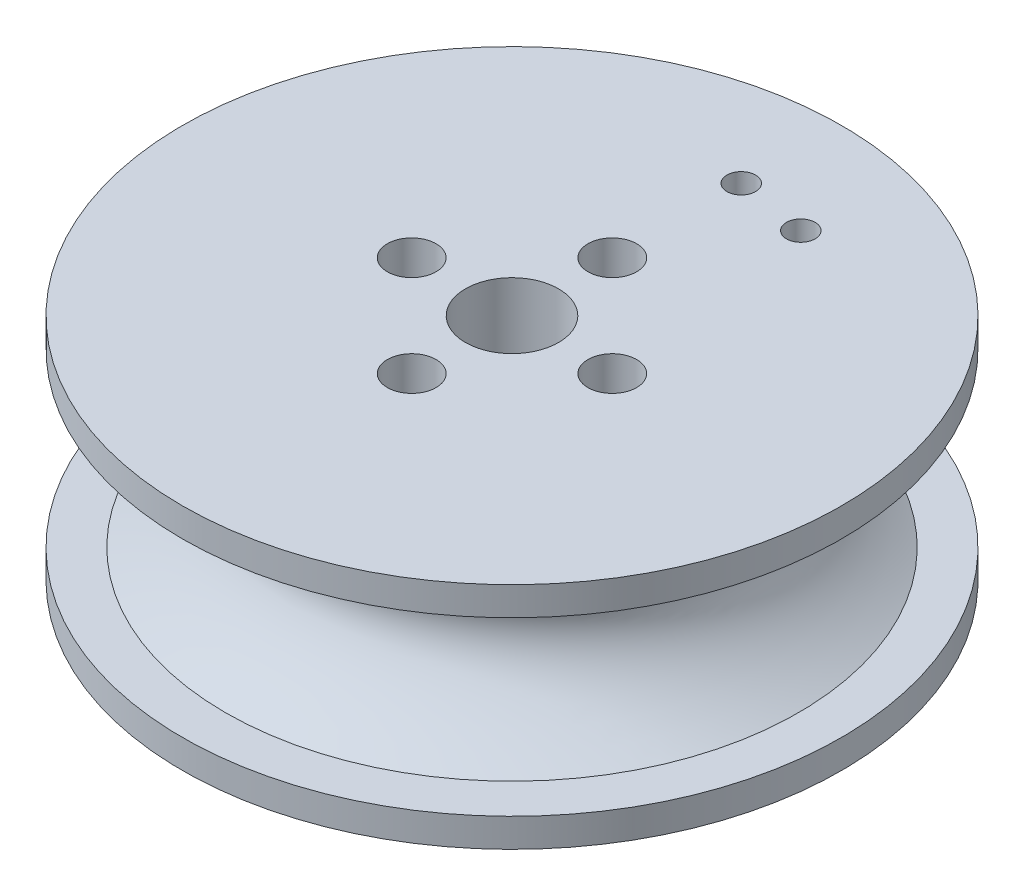
SolidWorks part; units mm, degrees
ref_plane "前视基准面" through (0, 0, 0) normal (0, 0, 1) x (1, 0, 0)
ref_plane "上视基准面" through (0, 0, 0) normal (0, 1, 0) x (1, 0, 0)
ref_plane "右视基准面" through (0, 0, 0) normal (1, 0, 0) x (0, 0, -1)
other "Configuration Table"
sketch "草图2" plane through (0, 0, 0) normal (0, 0, 1) x (1, 0, 0)
  line L0 (20, 6) -> (0, 6)
  line L1 (0, 6) -> (0, 0)
  line L2 (0, 0) -> (0, -6)
  line L3 (0, -6) -> (20, -6)
  spline S0 degree 2 poles (20, 6) (10, 0) (20, -6) knots 0 0 0 1 1 1
  dimension "D1" = 15
  dimension "D2" = 20
  dimension "D3" = 20
  dimension "D4" = 6
  dimension "D5" = 6
revolve "旋转1" add sketch "草图2" angle 360 about L1
sketch "草图3" plane through (0, 6, 0) normal (0, 1, 0) x (1, 0, 0)
  circle A0 centre (0, 0) radius 23
  dimension "D1" = 46
extrude "凸台-拉伸1" add sketch "草图3" along normal blind 2
sketch "草图4" plane through (0, -6, 0) normal (0, -1, 0) x (1, 0, 0)
  circle A0 centre (0, 0) radius 23
  circle A1 centre (0, 0) radius 23 construction
extrude "凸台-拉伸2" add sketch "草图4" along normal blind 2
hole_wizard "M3 间隙孔1" positions "草图5" profile "草图6" hole size "M3" standard "GB" end condition through all
sketch "草图5" plane through (0, 8, 0) normal (0, 1, 0) x (1, 0, 0)
  circle A0 centre (0, 0) radius 7
  point P5 (0, 7)
  point P7 (-7, 0)
  point P9 (7, 0)
  point P11 (0, -7)
  dimension "D1" = 14
sketch "草图6" plane through (0, 8, 7) normal (1, 0, 0) x (0, 0, 1)
  line L0 (0, 0) -> (0, 16)
  line L1 (0, 16) -> (1.7, 16)
  line L2 (1.7, 16) -> (1.7, 0)
  line L5 (1.7, 0) -> (0, 0)
  line L11 (0, -6.35) -> (0, 107.95) construction
  dimension "通孔孔直径" = 3.4
  dimension "通孔孔深度" = 16
sketch "Sketch1" plane through (0, 8, 0) normal (0, 1, 0) x (1, 0, 0)
  line L0 (0, 0) -> (0, 16) construction
  circle A0 centre (0, 16) radius 1
  circle A1 centre (0, 0) radius 15 construction
  circle A2 centre (0, 0) radius 15 construction
  circle A4 centre (0, 0) radius 3.25
  circle A5 centre (4.9386, 15.2188) radius 1
  dimension "D1" = 2
  dimension "D2" = 6.5
  dimension "D3" = 5
extrude "Cut-Extrude1" cut sketch "Sketch1" against normal through all
